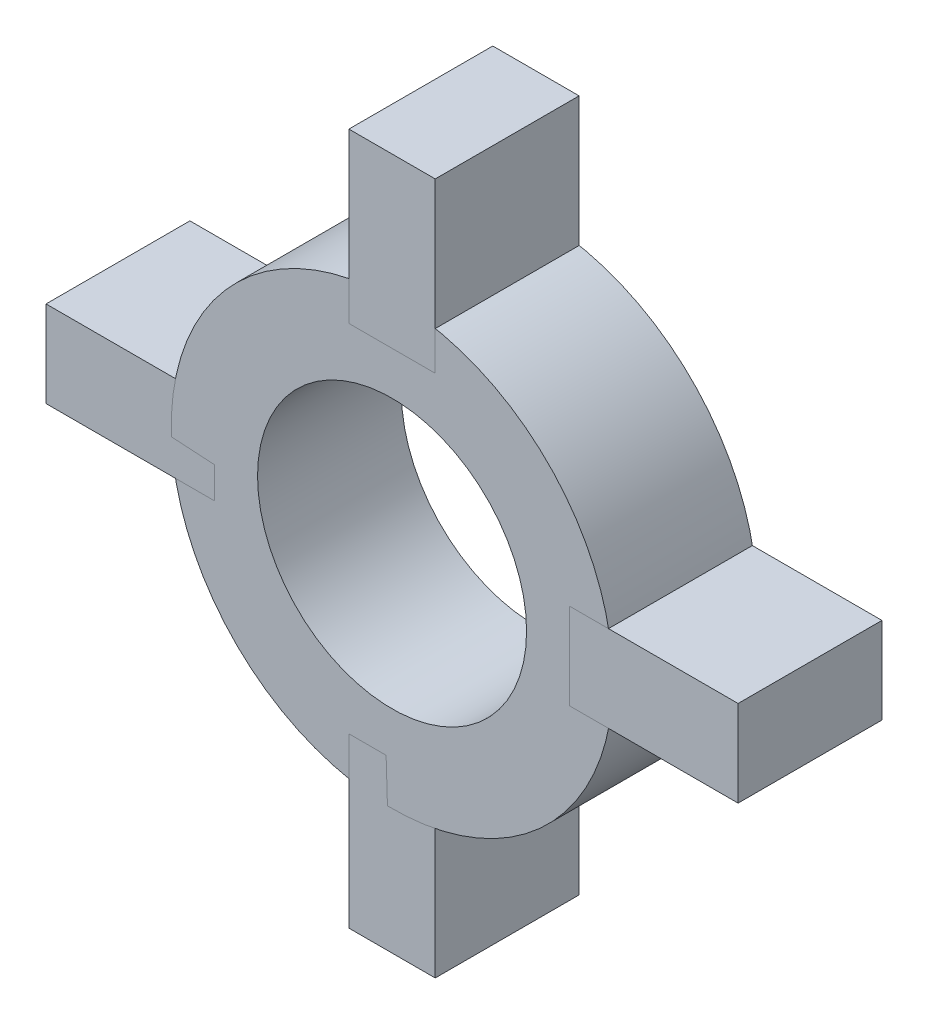
SolidWorks part; units mm, degrees
ref_plane "Front Plane" through (0, 0, 0) normal (0, 0, 1) x (1, 0, 0)
ref_plane "Top Plane" through (0, 0, 0) normal (0, 1, 0) x (1, 0, 0)
ref_plane "Right Plane" through (0, 0, 0) normal (1, 0, 0) x (0, 0, -1)
sketch "Sketch1" plane through (0, 0, 0) normal (0, 0, 1) x (1, 0, 0)
  line L0 (0, 6.175) -> (0, 12.025)
  line L1 (-19.0162, 0) -> (20.1075, 0) construction
  line L2 (0, -12.5518) -> (0, 15.6687) construction
  line L3 (0, -6.175) -> (0, -12.025)
  line L4 (6.175, 0) -> (12.025, 0)
  line L5 (-6.175, 0) -> (-12.025, 0)
  circle A0 centre (0, 0) radius 6.175
  dimension "D1" = 12.35
  dimension "D2" = 5.85
extrude "Extrude-Thin1" add sketch "Sketch1" along normal blind 5 thin thin type mid plane wall 3
